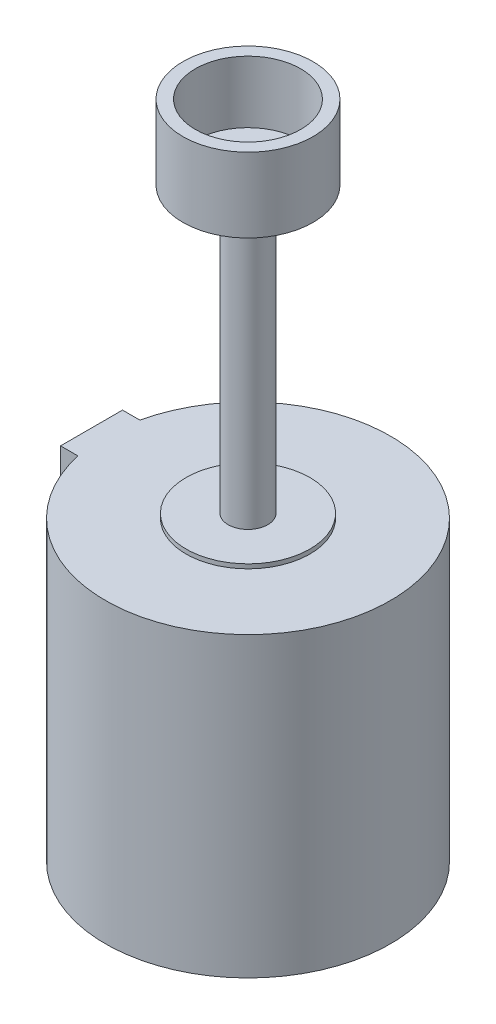
SolidWorks part; units mm, degrees
material "AISI 1020"
ref_plane "Front Plane" through (0, 0, 0) normal (0, 0, 1) x (1, 0, 0)
ref_plane "Top Plane" through (0, 0, 0) normal (0, 1, 0) x (1, 0, 0)
ref_plane "Right Plane" through (0, 0, 0) normal (1, 0, 0) x (0, 0, -1)
sketch "Sketch1" plane through (0, 0, 0) normal (0, 1, 0) x (1, 0, 0)
  circle A0 centre (0, 0) radius 16
  dimension "D1" = 32
extrude "Boss-Extrude1" add sketch "Sketch1" along normal blind 229.5
sketch "Sketch2" plane through (0, 229.5, 0) normal (0, 1, 0) x (1, 0, 0)
  circle A0 centre (0, 0) radius 52.5
  dimension "D1" = 105
extrude "Boss-Extrude2" add sketch "Sketch2" along normal blind 60
sketch "Sketch3" plane through (0, 289.5, 0) normal (0, 1, 0) x (1, 0, 0)
  circle A0 centre (0, 0) radius 42.5
  dimension "D1" = 85
extrude "Cut-Extrude1" cut sketch "Sketch3" against normal blind 50
sketch "Sketch6" plane through (0, 0, 0) normal (0, -1, 0) x (1, 0, 0)
  circle A0 centre (0, 0) radius 50
  dimension "D1" = 100
extrude "Boss-Extrude4" add sketch "Sketch6" along normal blind 3.5
sketch "Sketch7" plane through (0, -3.5, 0) normal (0, -1, 0) x (1, 0, 0)
  line L2 (-126.2797, -25) -> (-112.2497, -25)
  line L3 (-112.2497, 25) -> (-126.2797, 25)
  line L4 (-126.2797, 25) -> (-126.2797, -25)
  arc A1 (-112.2497, -25) -> (-112.2497, 25) centre (0, 0) ccw
  dimension "D1" = 50
  dimension "D2" = 230
  dimension "D4" = 14.03
extrude "Boss-Extrude5" add sketch "Sketch7" along normal blind 240
sketch "Sketch8" plane through (0, -243.5, 0) normal (0, -1, 0) x (1, 0, 0)
  circle A0 centre (0, 0) radius 110
  dimension "D1" = 220
extrude "Cut-Extrude3" cut sketch "Sketch8" against normal blind 50
